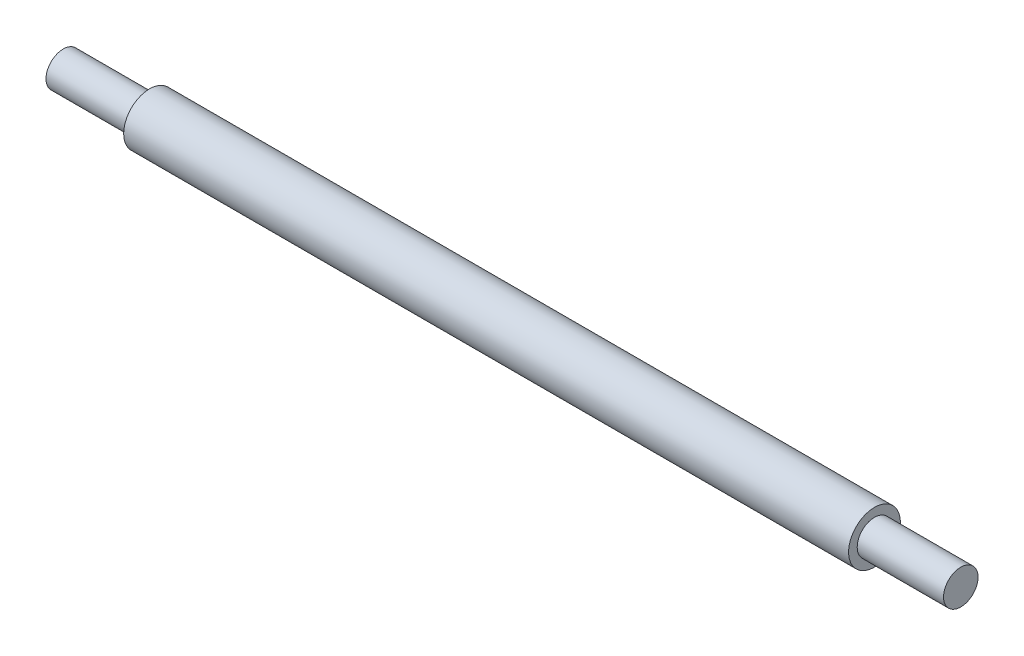
SolidWorks part; units mm, degrees
ref_plane "Front" through (0, 0, 0) normal (0, 0, 1) x (1, 0, 0)
ref_plane "Top" through (0, 0, 0) normal (0, 1, 0) x (1, 0, 0)
ref_plane "Right" through (0, 0, 0) normal (1, 0, 0) x (0, 0, -1)
sketch "Sketch1" plane through (0, 0, 0) normal (0, 0, 1) x (1, 0, 0)
  line L0 (0, 0) -> (0, 2)
  line L1 (0, 2) -> (10, 2)
  line L2 (10, 2) -> (10, 3)
  line L3 (10, 3) -> (94, 3)
  line L4 (94, 3) -> (94, 2)
  line L5 (94, 2) -> (104, 2)
  line L6 (104, 2) -> (104, 0)
  line L7 (-71.6876, 0) -> (131.7216, 0) construction
  line L8 (10, 2) -> (10, 0)
  line L9 (94, 2) -> (94, 0)
  dimension "D1" = 104
  dimension "D2" = 10
  dimension "D3" = 2
  dimension "D4" = 3
  dimension "D5" = 10
revolve "Revolve1" add sketch "Sketch1" angle 360 about L7
